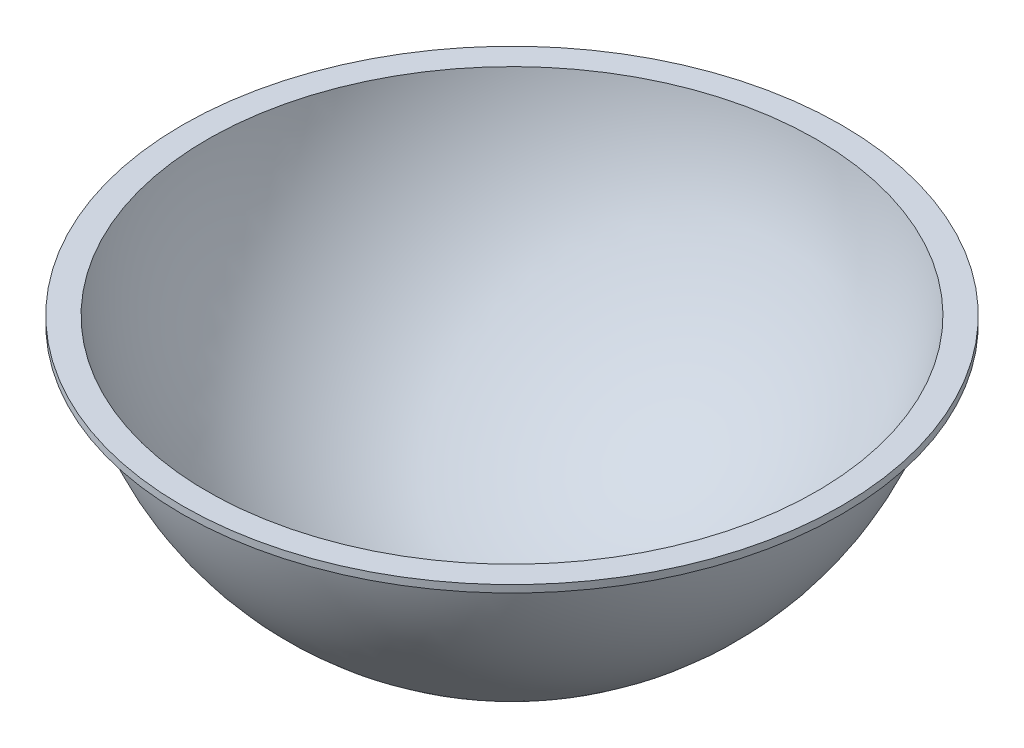
SolidWorks part; units mm, degrees
ref_plane "Alzado" through (0, 0, 0) normal (0, 0, 1) x (1, 0, 0)
ref_plane "Planta" through (0, 0, 0) normal (0, 1, 0) x (1, 0, 0)
ref_plane "Vista lateral" through (0, 0, 0) normal (1, 0, 0) x (0, 0, -1)
sketch "Croquis1" plane through (0, 0, 0) normal (1, 0, 0) x (0, 0, -1)
  line L0 (0, 0) -> (0, 88.9) construction
  line L1 (0, 88.9) -> (107.95, 88.9) construction
  line L2 (107.95, 88.9) -> (114.5044, 88.9)
  line L3 (105.8376, 91.44) -> (114.5044, 91.44)
  line L4 (114.5044, 91.44) -> (114.5044, 88.9)
  line L5 (0, 0) -> (0, 2.54)
  arc A0 (0, 0) -> (107.95, 88.9) centre (0, 109.9911) ccw
  arc A1 (0, 2.54) -> (105.8376, 91.44) centre (0, 109.9911) ccw
  dimension "D1" = 88.9
  dimension "D2" = 107.95
  dimension "D3" = 2.54
revolve "Revolución2" add sketch "Croquis1" angle 360 about L0
